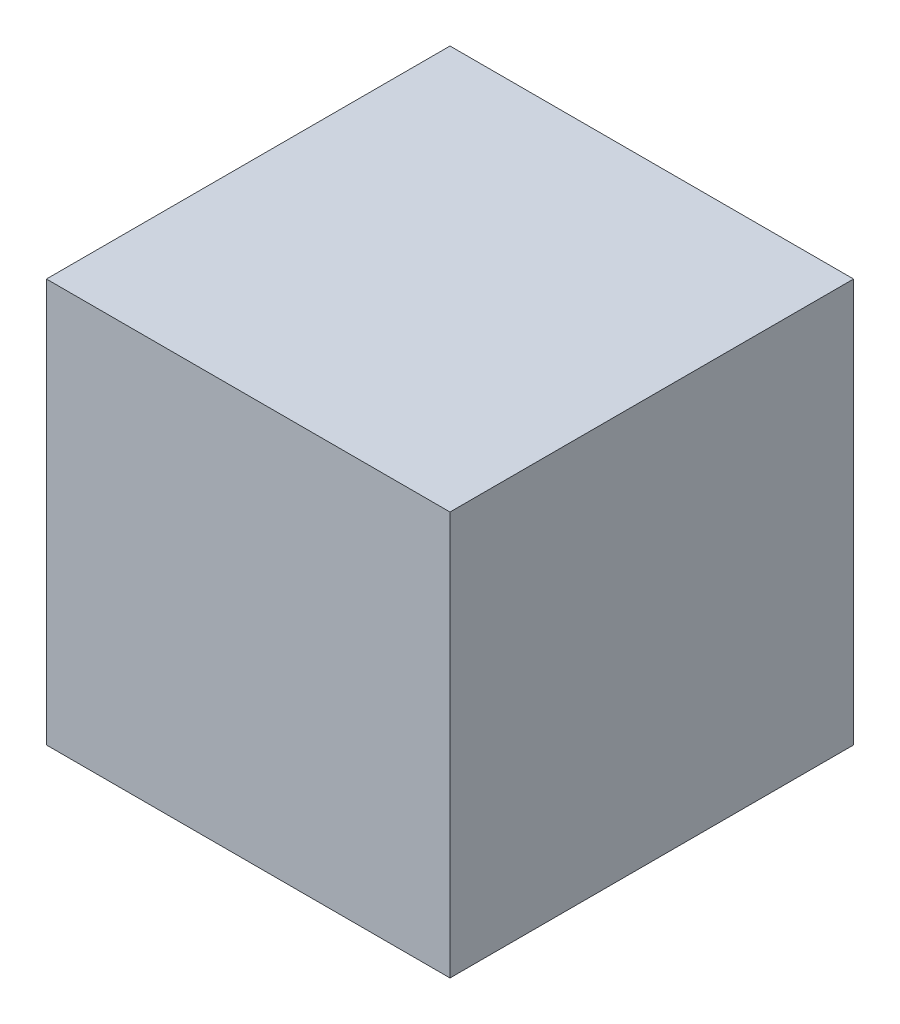
SolidWorks part; units mm, degrees
ref_plane "Front Plane" through (0, 0, 0) normal (0, 0, 1) x (1, 0, 0)
ref_plane "Top Plane" through (0, 0, 0) normal (0, 1, 0) x (1, 0, 0)
ref_plane "Right Plane" through (0, 0, 0) normal (1, 0, 0) x (0, 0, -1)
sketch "Sketch1" plane through (0, 0, 0) normal (0, 0, 1) x (1, 0, 0)
  line L0 (-10, 10) -> (190, 10)
  line L2 (-10, 10) -> (-10, -190)
  line L3 (-10, -190) -> (190, -190)
  line L4 (190, -190) -> (190, 10)
  dimension "D1" = 200
  dimension "D2" = 200
extrude "Boss-Extrude1" add sketch "Sketch1" along normal blind 200
